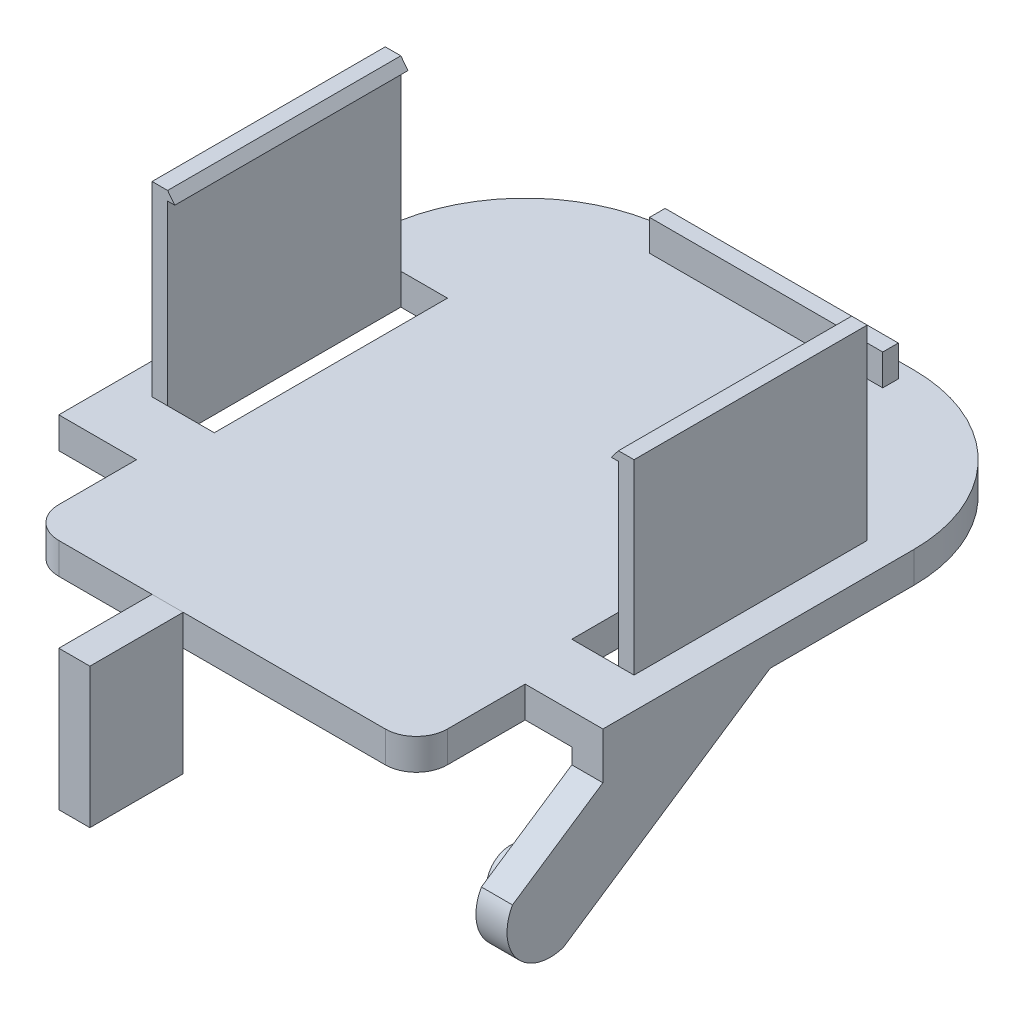
SolidWorks part; units mm, degrees
ref_plane "Front Plane" through (0, 0, 0) normal (0, 0, 1) x (1, 0, 0)
ref_plane "Top Plane" through (0, 0, 0) normal (0, 1, 0) x (1, 0, 0)
ref_plane "Right Plane" through (0, 0, 0) normal (1, 0, 0) x (0, 0, -1)
sketch "Sketch1" plane through (0, 0, 0) normal (0, 1, 0) x (1, 0, 0)
  line L1 (-17.5, 18.5) -> (17.5, 18.5)
  line L2 (-17.5, 18.5) -> (-17.5, -18.5)
  line L3 (-17.5, -18.5) -> (17.5, -18.5)
  line L4 (17.5, 18.5) -> (17.5, -18.5)
  line L5 (-17.5, 18.5) -> (17.5, -18.5) construction
  line L6 (-17.5, -18.5) -> (17.5, 18.5) construction
  point P0 (0, 0)
  dimension "D1" = 37
  dimension "D2" = 35
extrude "Boss-Extrude1" add sketch "Sketch1" along normal blind 2
fillet "Fillet1" radius 10 2 edges at (-17.5, 1, -18.5) (17.5, 1, -18.5)
sketch "Sketch2" plane through (0, 2, 0) normal (0, 1, 0) x (1, 0, 0)
  line L0 (7.5, 18.5) -> (-7.5, 18.5) construction
  line L1 (-7.5, 17.5) -> (7.5, 17.5)
  line L2 (-7.5, 17.5) -> (-7.5, 16.5)
  line L3 (-7.5, 16.5) -> (7.5, 16.5)
  line L4 (7.5, 17.5) -> (7.5, 16.5)
  line L5 (-7.5, 17.5) -> (7.5, 16.5) construction
  line L6 (-7.5, 16.5) -> (7.5, 17.5) construction
  line L7 (0, 30.6529) -> (0, -32.3661) construction
  point P0 (0, 17)
  dimension "D1" = 15
  dimension "D2" = 1
  dimension "D3" = 1
  dimension "D4" = 0
extrude "Boss-Extrude2" add sketch "Sketch2" along normal blind 2
sketch "Sketch3" plane through (0, 2, 0) normal (0, 1, 0) x (1, 0, 0)
  line L0 (17.5, -11.5) -> (12.5, -11.5)
  line L1 (12.5, -11.5) -> (12.5, -18.5)
  line L2 (-17.5, -11.5) -> (-12.5, -11.5)
  line L3 (-12.5, -11.5) -> (-12.5, -18.5)
  line L4 (7.5, 18.5) -> (-7.5, 18.5)
  line L5 (-17.5, 8.5) -> (-17.5, -18.5)
  line L6 (-17.5, -18.5) -> (17.5, -18.5)
  line L7 (17.5, -18.5) -> (17.5, 8.5)
  line L9 (-17.5, -11.5) -> (-17.5, -18.5)
  line L10 (-17.5, -18.5) -> (-12.5, -18.5)
  line L11 (17.5, -18.5) -> (17.5, -11.5)
  line L12 (12.5, -18.5) -> (17.5, -18.5)
  arc A2 (-7.5, 18.5) -> (-17.5, 8.5) centre (-7.5, 8.5) ccw
  arc A3 (17.5, 8.5) -> (7.5, 18.5) centre (7.5, 8.5) ccw
  dimension "D2" = 7
  dimension "D3" = 5
  dimension "D1" = 0
extrude "Cut-Extrude1" cut sketch "Sketch3" against normal up to next
fillet "Fillet2" radius 2 2 edges at (-12.5, 1, 18.5) (12.5, 1, 18.5)
sketch "Sketch4" plane through (17.5, 0, 0) normal (1, 0, 0) x (0, 0, -1)
  line L0 (-11.5, 0) -> (-11.5, -1)
  line L1 (-11.5, -1) -> (-17.3176, -4.8931)
  line L2 (-14.047, -8.8985) -> (-0.7497, 0)
  line L3 (-11.5, 0) -> (8.5, 0) construction
  line L4 (-11.5, 0) -> (-0.7497, 0)
  arc A0 (-17.3176, -4.8931) -> (-14.047, -8.8985) centre (-14.8886, -6.2477) ccw
  point P0 (-0.7579, 0)
extrude "Boss-Extrude3" add sketch "Sketch4" against normal blind 2
sketch "Sketch5" plane through (17.5, 0, 0) normal (1, 0, 0) x (0, 0, -1)
  line L0 (-11.5, -1) -> (-17.3176, -4.8931) construction
  circle A0 centre (-14.4765, -6) radius 1.5
  dimension "D1" = 3
  dimension "D2" = 2.5
  dimension "D3" = 5
extrude "Boss-Extrude4" add sketch "Sketch5" against normal blind 3
sketch "Sketch6" plane through (0, 2, 0) normal (0, 1, 0) x (1, 0, 0)
  line L0 (0, 23.6319) -> (0, -42.1457) construction
  line L5 (14.5, 7.5) -> (15.5, 7.5)
  line L6 (14.5, 7.5) -> (14.5, -7.5)
  line L7 (14.5, -7.5) -> (15.5, -7.5)
  line L8 (15.5, 7.5) -> (15.5, -7.5)
  line L9 (14.5, 7.5) -> (15.5, -7.5) construction
  line L10 (14.5, -7.5) -> (15.5, 7.5) construction
  line L11 (17.5, -11.5) -> (12.5, -11.5) construction
  line L12 (17.5, -11.5) -> (17.5, 8.5) construction
  line L13 (-14.5, -7.5) -> (-15.5, 7.5) construction
  line L14 (-14.5, 7.5) -> (-15.5, -7.5) construction
  line L15 (-15.5, 7.5) -> (-15.5, -7.5)
  line L16 (-14.5, -7.5) -> (-15.5, -7.5)
  line L17 (-14.5, 7.5) -> (-14.5, -7.5)
  line L18 (-14.5, 7.5) -> (-15.5, 7.5)
  point P0 (15, 0)
  point P16 (-15, 0)
  dimension "D1" = 1
  dimension "D2" = 15
  dimension "D3" = 4
  dimension "D4" = 2
extrude "Boss-Extrude5" add sketch "Sketch6" along normal blind 12
sketch "Sketch7" plane through (0, 0, 7.5) normal (0, 0, 1) x (1, 0, 0)
  line L0 (-14.5, 14) -> (-14.0371, 13.4083)
  line L1 (-14.0371, 13.4083) -> (-14.5, 13.4083)
  line L4 (-15.5, 2) -> (-14.5, 2)
  line L5 (-14.5, 2) -> (-14.5, 14)
  line L6 (-14.5, 14) -> (-15.5, 14)
  line L7 (-15.5, 14) -> (-15.5, 2)
  line L9 (-14.5, 13.4083) -> (-14.5, 14)
  point P2 (0, 0)
  dimension "D1" = 0
extrude "Boss-Extrude6" add sketch "Sketch7" against normal up to surface (15 mm away) up to face at (-15, 8, -7.5)
mirror "Mirror1" about plane through (0, 0, 0) normal (1, 0, 0) of "Boss-Extrude6"
sketch "Sketch8" plane through (0, 2, 0) normal (0, 1, 0) x (1, 0, 0)
  line L0 (-14.5, 7.5) -> (-11.5, 7.5)
  line L1 (-11.5, 7.5) -> (-11.5, -7.5)
  line L2 (-11.5, -7.5) -> (-14.5, -7.5)
  line L3 (-14.5, -7.5) -> (-14.5, 7.5)
  dimension "D2" = 3
extrude "Cut-Extrude4" cut sketch "Sketch8" against normal up to next (2 mm away)
mirror "Mirror2" about plane through (0, 0, 0) normal (1, 0, 0) of "Cut-Extrude4"
sketch "Sketch11" plane through (0, 2, 0) normal (0, 1, 0) x (1, 0, 0)
  line L5 (-10.5, -18.5) -> (10.5, -18.5) construction
  line L6 (-2.5, -18.5) -> (-4.5, -18.5)
  line L7 (-2.5, -18.5) -> (-2.5, -24.5)
  line L8 (-2.5, -24.5) -> (-4.5, -24.5)
  line L9 (-4.5, -18.5) -> (-4.5, -24.5)
  dimension "D1" = 6
  dimension "D2" = 2
  dimension "D3" = 6
extrude "Boss-Extrude8" add sketch "Sketch11" against normal blind 9 separate body
